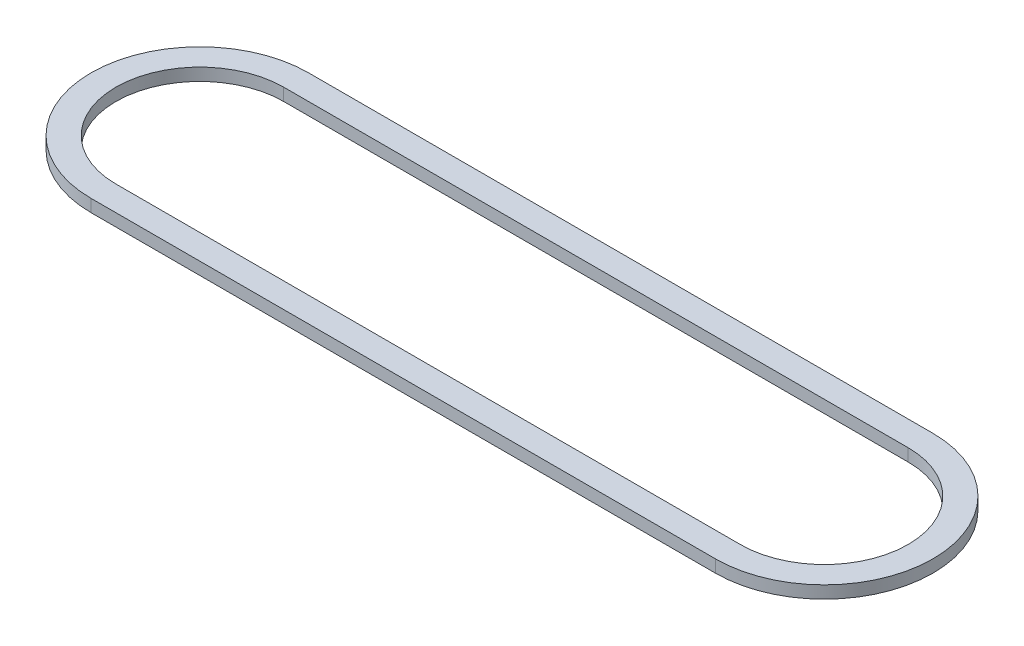
SolidWorks part; units mm, degrees
material "NBR"
ref_plane "Front Plane" through (0, 0, 0) normal (0, 0, 1) x (1, 0, 0)
ref_plane "Top Plane" through (0, 0, 0) normal (0, 1, 0) x (1, 0, 0)
ref_plane "Right Plane" through (0, 0, 0) normal (1, 0, 0) x (0, 0, -1)
sketch "Sketch1" plane through (0, 0, 0) normal (0, 1, 0) x (1, 0, 0)
  line L0 (-12.7635, 0) -> (12.7635, 0) construction
  line L1 (-12.7635, 3.429) -> (12.7635, 3.429)
  line L2 (-12.7635, -3.429) -> (12.7635, -3.429)
  line L3 (-12.7635, 0) -> (12.7635, 0) construction
  line L4 (-12.7635, 4.445) -> (12.7635, 4.445)
  line L5 (-12.7635, -4.445) -> (12.7635, -4.445)
  arc A0 (-12.7635, 3.429) -> (-12.7635, -3.429) centre (-12.7635, 0) ccw
  arc A1 (12.7635, -3.429) -> (12.7635, 3.429) centre (12.7635, 0) ccw
  arc A2 (-12.7635, 4.445) -> (-12.7635, -4.445) centre (-12.7635, 0) ccw
  arc A3 (12.7635, -4.445) -> (12.7635, 4.445) centre (12.7635, 0) ccw
  point P2 (0, 0)
  point P9 (0, 0)
  dimension "D2" = 4.445
  dimension "D1" = 1.016
  dimension "D3" = 25.527
extrude "Boss-Extrude1" add sketch "Sketch1" along normal blind 0.508
equation "\"w\"= 0.04"
equation "\"D2@Sketch1\" = .185 - .01'10 thou smaller than channel rad"
equation "\"D1@Sketch1\"=\"w\""
